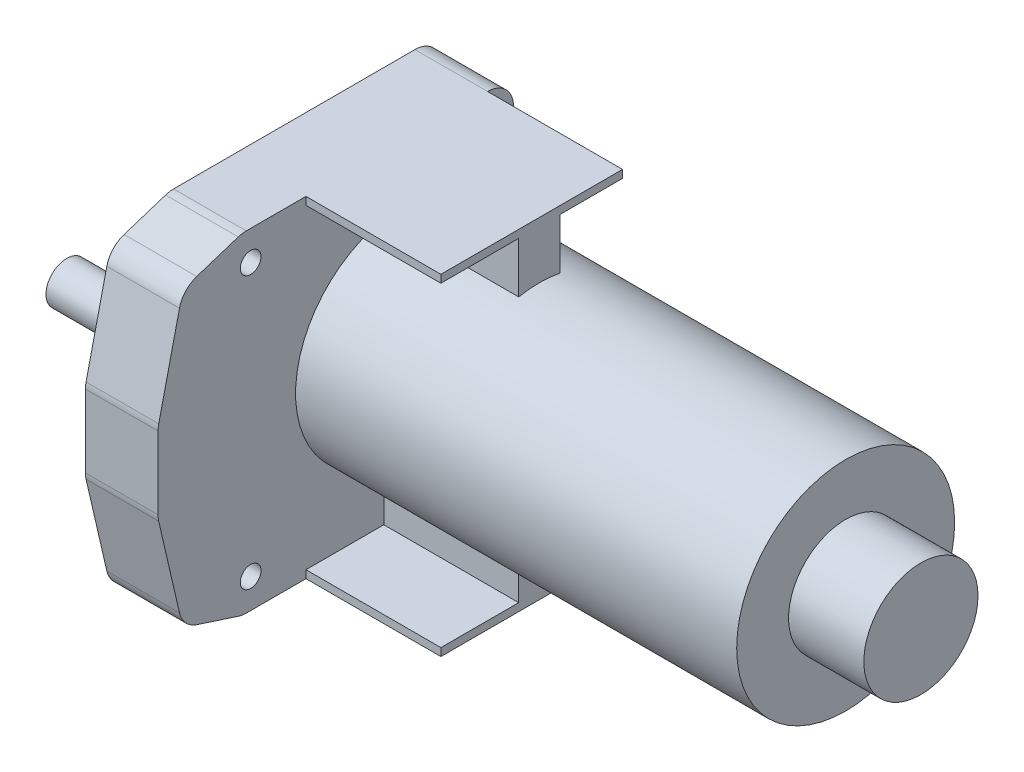
SolidWorks part; units mm, degrees
material "AISI 1020"
ref_plane "Plan de face" through (0, 0, 0) normal (0, 0, 1) x (1, 0, 0)
ref_plane "Plan de dessus" through (0, 0, 0) normal (0, 1, 0) x (1, 0, 0)
ref_plane "Plan de droite" through (0, 0, 0) normal (1, 0, 0) x (0, 0, -1)
sketch "Esquisse1" plane through (0, 0, 0) normal (1, 0, 0) x (0, 0, -1)
  line L0 (67.8364, 0) -> (-61.451, 0) construction
  line L3 (-6, 31.9) -> (40.5, 31.9)
  line L4 (-15.5448, 29.0565) -> (-7.5448, 31.6554)
  line L5 (-22.8716, 8.1188) -> (-18.8716, 25.427)
  line L18 (-23, 6.993) -> (-23, -6.993)
  line L19 (-22.8716, -8.1188) -> (-18.8716, -25.427)
  line L20 (-15.5448, -29.0565) -> (-7.5448, -31.6554)
  line L21 (-6, -31.9) -> (40.5, -31.9)
  line L22 (45.5, -26.9) -> (45.5, 26.9)
  arc A0 (40.5, 31.9) -> (45.5, 26.9) centre (40.5, 26.9) cw
  arc A1 (-7.5448, 31.6554) -> (-6, 31.9) centre (-6, 26.9) cw
  arc A2 (-18.8716, 25.427) -> (-15.5448, 29.0565) centre (-14, 24.3011) cw
  arc A3 (-23, 6.993) -> (-22.8716, 8.1188) centre (-18, 6.993) cw
  circle A4 centre (38.44, -26.2) radius 2
  circle A5 centre (-5.16, -26.2) radius 2
  circle A6 centre (-5.16, 26.2) radius 2
  circle A7 centre (38.44, 26.2) radius 2
  arc A19 (-23, -6.993) -> (-22.8716, -8.1188) centre (-18, -6.993) ccw
  arc A20 (-18.8716, -25.427) -> (-15.5448, -29.0565) centre (-14, -24.3011) ccw
  arc A21 (-7.5448, -31.6554) -> (-6, -31.9) centre (-6, -26.9) ccw
  arc A22 (40.5, -31.9) -> (45.5, -26.9) centre (40.5, -26.9) ccw
  dimension "D5" = 5
  dimension "D6" = 43.6
  dimension "D9" = 9
  dimension "D7" = 4
  dimension "D1" = 63.8
  dimension "D2" = 68.5
  dimension "D3" = 23
  dimension "D4" = 13.9859
  dimension "D8" = 24.3011
  dimension "D10" = 17
  dimension "D11" = 52.4
  dimension "D12" = 5.16
extrude "Extrusion3" add sketch "Esquisse1" along normal blind 14
sketch "Esquisse3" plane through (14, 0, 0) normal (1, 0, 0) x (0, 0, -1)
  circle A0 centre (24.5, 0) radius 21
  dimension "D1" = 42
  dimension "D2" = 24.5
extrude "Extrusion4" add sketch "Esquisse3" along normal blind 85
sketch "Esquisse4" plane through (0, 0, 0) normal (1, 0, 0) x (0, 0, -1)
  circle A0 centre (0, 0) radius 4
  dimension "D1" = 8
extrude "Extrusion5" add sketch "Esquisse4" against normal blind 26.6
sketch "Esquisse5" plane through (0, 0, 0) normal (1, 0, 0) x (0, 0, -1)
  circle A0 centre (0, 0) radius 7.25
  dimension "D1" = 14.5
extrude "Extrusion6" add sketch "Esquisse5" against normal blind 5
sketch "Esquisse6" plane through (99, 0, 0) normal (1, 0, 0) x (0, 0, -1)
  line L0 (24.5, 14) -> (24.5, 21)
  line L1 (24.5, -14) -> (24.5, -21)
  arc A0 (24.5, 21) -> (24.5, -21) centre (24.5, 0) cw
  circle A1 centre (24.5, 0) radius 21 construction
  arc A2 (24.5, -14) -> (24.5, 14) centre (24.5, 0) cw
  dimension "D1" = 14
extrude "Extrusion7" [suppressed] add sketch "Esquisse6" along normal blind 18
sketch "Esquisse7" [suppressed] plane through (117, 0, 0) normal (1, 0, 0) x (0, 0, -1)
  line L0 (43.9165, 8) -> (34.5, 8)
  line L1 (34.5, 8) -> (34.5, -8)
  line L2 (34.5, -8) -> (43.9165, -8)
  arc A0 (43.9165, 8) -> (43.9165, -8) centre (24.5, 0) cw
  arc A1 (24.5, -21) -> (24.5, 21) centre (24.5, 0) ccw construction
  dimension "D1" = 16
  dimension "D2" = 11
extrude "Extrusion8" [suppressed] add sketch "Esquisse7" along normal blind 5
sketch "Esquisse8" plane through (14, 0, 0) normal (1, 0, 0) x (0, 0, -1)
  line L0 (40.5, 31.9) -> (5.5, 31.9)
  line L1 (40.5, 31.9) -> (-6, 31.9) construction
  line L2 (5.5, 31.9) -> (5.5, 30.4)
  line L3 (5.5, 30.4) -> (20.5, 30.4)
  line L4 (20.5, 30.4) -> (20.5, 13.1472)
  line L5 (20.5, 13.1472) -> (28.5, 13.1472)
  line L6 (28.5, 13.1472) -> (28.5, 30.4)
  line L7 (28.5, 30.4) -> (40.5, 30.4)
  line L8 (40.5, 30.4) -> (40.5, 31.9)
  line L9 (24.5, 11.1603) -> (24.5, -22.6325) construction
  line L10 (40.5, 0) -> (-9.3952, 0) construction
  line L11 (40.5, -30.4) -> (40.5, -31.9)
  line L12 (28.5, -30.4) -> (40.5, -30.4)
  line L13 (28.5, -13.1472) -> (28.5, -30.4)
  line L14 (20.5, -13.1472) -> (28.5, -13.1472)
  line L15 (20.5, -30.4) -> (20.5, -13.1472)
  line L16 (5.5, -30.4) -> (20.5, -30.4)
  line L17 (5.5, -31.9) -> (5.5, -30.4)
  line L18 (40.5, -31.9) -> (5.5, -31.9)
  circle A0 centre (24.5, 0) radius 21 construction
  point P7 (24.5, 0)
  dimension "D1" = 1.5
  dimension "D2" = 35
  dimension "D3" = 8
extrude "Extrusion9" add sketch "Esquisse8" along normal blind 26
sketch "Esquisse9" plane through (99, 0, 0) normal (1, 0, 0) x (0, 0, -1)
  circle A0 centre (24.5, 0) radius 11
  dimension "D1" = 22
extrude "Extrusion10" add sketch "Esquisse9" along normal blind 14.5
ref_point "Point1"
ref_point "Point2"
